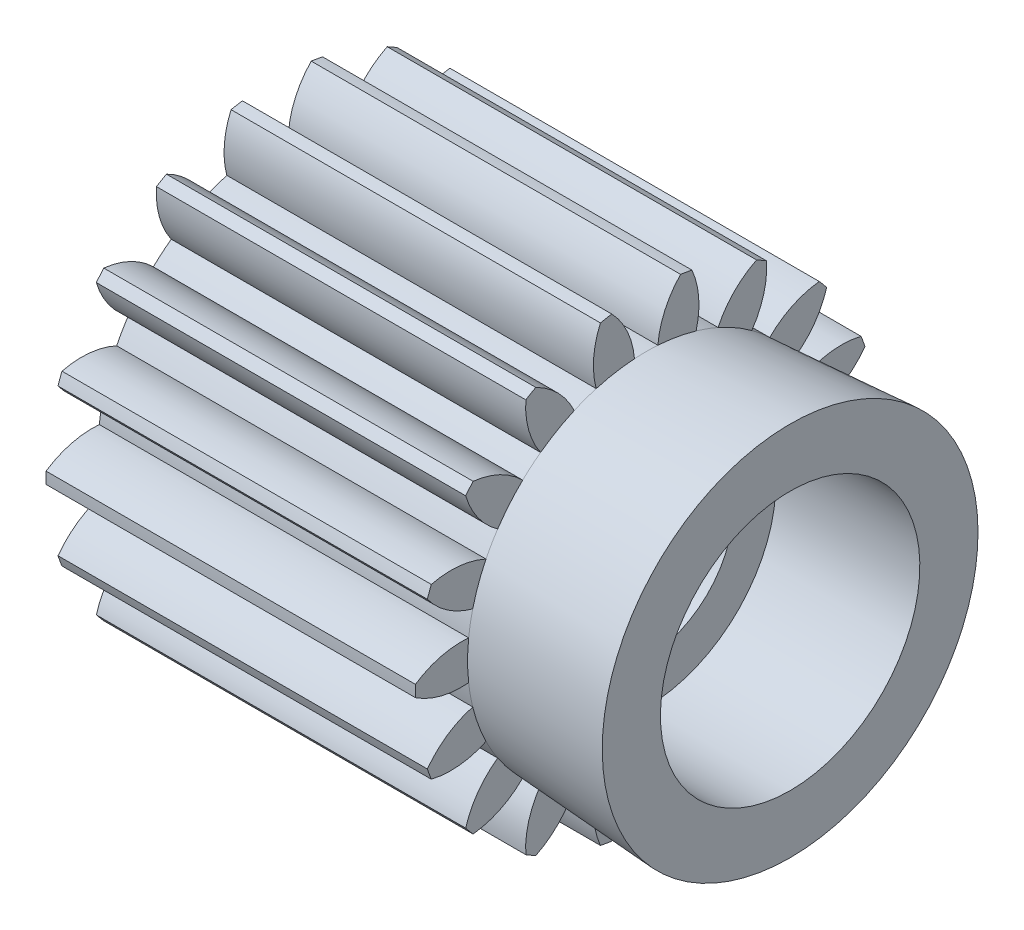
SolidWorks part; units mm, degrees
ref_plane "Plane1" through (0, 0, 0) normal (0, 0, 1) x (1, 0, 0)
ref_plane "Plane2" through (0, 0, 0) normal (0, 1, 0) x (1, 0, 0)
ref_plane "Plane3" through (0, 0, 0) normal (1, 0, 0) x (0, 0, -1)
sketch "HoldingSke" plane through (0, 0, 0) normal (0, 1, 0) x (1, 0, 0)
  line L0 (0, 0) -> (773.0187, -251.169)
  line L1 (-15, 0) -> (100, 0) construction
  line L2 (0, 0) -> (-2.1039, 2.3779)
  line L3 (0, 0) -> (-11.863, 4.5341)
  line L4 (0, 0) -> (8.2133, 2.6687)
  line L5 (0, 0) -> (-47.5972, -17.7524)
  line L6 (0, 0) -> (-10.5278, -7.1032)
  line L7 (-2.1039, 2.3779) -> (8.8308, 51.9871)
  line L8 (-76.2, 54.61) -> (-69.596, 54.61)
  line L9 (-71.009, 38.7566) -> (-53.1078, 45.2721)
  line L10 (-76.2, 71.12) -> (104.1128, 71.12)
  line L11 (0, 0) -> (-12.7, 0)
  line L12 (-76.2, 101.6) -> (-76.1716, 101.6)
  line L13 (24.9733, 27.94) -> (52.9518, 28.4284)
  line L14 (24.9733, 27.94) -> (25.0241, 27.9398)
  line L15 (24.9733, 27.94) -> (100.4021, 29.52)
  circle A0 centre (0, 0) radius 3.175
  circle A1 centre (0, 0) radius 6.1404
  circle A2 centre (0, 0) radius 38.1
  circle A3 centre (0, 0) radius 3.175
  dimension "MHD" = 12.2809
  dimension "Hub_dia" = 76.2
  dimension "Bore" = 6.35
  dimension "MBD" = 6.35
  dimension "Num_teeth" = 18
  dimension "Pitch" = 812.8
  dimension "Overall_len" = 50.8
  dimension "Show_teeth" = 18
  dimension "Thickness" = 12.7
  dimension "OAL" = 50.8001
  dimension "T_dim" = 6.604
  dimension "Ap" = 20
  dimension "H" = 19.05
  dimension "Pitch_radius" = 180.3128
  dimension "Width" = 12.7
  dimension "Backlash" = 0.0284
  dimension "Addendum_fac" = 1
  dimension "Dedendum_fac" = 1.2
  dimension "Clearance_fac" = 0.2
  dimension "Dedendum_add" = 0.0508
sketch "BasProSke" plane through (0, 0, 0) normal (0, 1, 0) x (1, 0, 0)
  line L0 (-10, 0) -> (60, 0) construction
  line L1 (0, 0) -> (0, 7.9375)
  line L2 (0, 0) -> (12.7, 0)
  line L3 (12.7, 0) -> (12.7, 7.9375)
  line L4 (12.7, 7.9375) -> (0, 7.9375)
  dimension "Thickness" = 12.7
  dimension "Diameter" = 15.875
revolve "Base-Revolve" add sketch "BasProSke" angle 360 about L0
sketch "TooCutSke" plane through (0, 0, 0) normal (1, 0, 0) x (0, 0, -1)
  line L1 (0, 0) -> (0, 107) construction
  line L2 (0, 0) -> (-0.6724, 7.112) construction
  line L3 (0, 0) -> (-2.473, 14.0251) construction
  line L4 (-0.6724, 7.112) -> (-1.2365, 7.0126) construction
  arc A0 (0.4018, 6.1273) -> (-0.4018, 6.1273) centre (0, 0) ccw
  arc A1 (1.2039, 7.8714) -> (-1.2039, 7.8714) centre (0, 0) ccw
  circle A2 centre (0, 0) radius 7.1438 construction
  circle A3 centre (0, 0) radius 6.7129 construction
  arc A4 (-0.4018, 6.1273) -> (-1.2039, 7.8714) centre (-3.2481, 5.8748) ccw
  arc A5 (1.2039, 7.8714) -> (0.4018, 6.1273) centre (3.2481, 5.8748) ccw
  dimension "Root_dia" = 12.2809
  dimension "Overcut_dia" = 15.9258
  dimension "Pitch_dia" = 14.2875
  dimension "Base_dia" = 13.4259
  dimension "Flank_rad" = 2.8575
  dimension "Half_ang" = 10
  dimension "Half_CT" = 0.5728
extrude "ToothCut" cut sketch "TooCutSke" along normal through all
fillet "Breaks" [suppressed] radius 0.0159
fillet "RootFillets" [suppressed] radius 0.2095
pattern_circular "TeethCuts" count 18 every 20 about axis through (-10, 0, 0) along (1, 0, 0) of "ToothCut", "RootFillets", "Breaks"
sketch "HubNeaOneSke" plane through (0, 0, 0) normal (-1, 0, 0) x (0, 0, 1)
  circle A0 centre (0, 0) radius 6.1404
  dimension "Diameter" = 12.2809
extrude "HubNearOne" [suppressed] add sketch "HubNeaOneSke" along normal blind 38.1001
sketch "HubNeaBotSke" plane through (0, 0, 0) normal (-1, 0, 0) x (0, 0, 1)
  circle A0 centre (0, 0) radius 6.1404
  dimension "Diameter" = 12.2809
extrude "HubNearBoth" [suppressed] add sketch "HubNeaBotSke" along normal blind 19.05
ref_plane "FarPln" through (12.7, 0, 0) normal (1, 0, 0) x (0, 0, -1)
sketch "HubFarSke" plane through (12.7, 0, 0) normal (1, 0, 0) x (0, 0, -1)
  circle A0 centre (0, 0) radius 6.1404
  dimension "Diameter" = 12.2809
extrude "HubFar" [suppressed] add sketch "HubFarSke" along normal blind 19.05
sketch "BorSke" plane through (0, 0, 0) normal (1, 0, 0) x (0, 0, -1)
  circle A0 centre (0, 0) radius 3
  dimension "D1" = 6
extrude "Bore" cut sketch "BorSke" along normal mid plane 101.6001
sketch "KeySke" plane through (0, 0, 0) normal (1, 0, 0) x (0, 0, -1)
  line L0 (-0.127, 0) -> (-0.127, 3.429)
  line L1 (-0.127, 3.429) -> (0.127, 3.429)
  line L2 (0.127, 3.429) -> (0.127, 0)
  line L3 (0, 0) -> (0, 34) construction
  line L4 (-0.127, 0) -> (0.127, 0)
  dimension "Offset" = 3.429
  dimension "Width" = 0.254
extrude "Keyway" [suppressed] cut sketch "KeySke" along normal mid plane 101.6001
pattern_circular "Keyway2" [suppressed] count 2 every 90 about axis through (-10, 0, 0) along (1, 0, 0)
sketch "Sketch1" plane through (0, 0, 0) normal (0, 0, 1) x (1, 0, 0)
  line L0 (12.7, 6.1405) -> (17.65, 6.46)
  line L1 (17.65, 6.46) -> (17.65, 4.46)
  line L2 (17.65, 4.46) -> (12.7, 4.46)
  line L3 (12.7, 4.9483) -> (12.7, 5.2527) construction
  line L4 (12.7, 0) -> (13.683, 0) construction
  line L5 (12.7, -0.1987) -> (12.7, 0.1987) construction
  line L6 (12.7, 4.46) -> (12.7, 6.1405)
  line L7 (12.7, 5.8952) -> (12.7, 7.78) construction
  point P3 (0, 0)
  point P8 (12.7, 7.2775)
  point P16 (12.7, 5.9593)
  point P18 (17.6948, 6.46)
  dimension "D1" = 4.46
  dimension "D2" = 2
  dimension "D3" = 4.95
revolve "Revolve1" add sketch "Sketch1" angle 360 about L4
equation "' \"Pitch@HoldingSke\" = 4"
equation "' \"Num_teeth@HoldingSke\" = 12"
equation "' \"Ap@HoldingSke\" =  20"
equation "' \"Ap@HoldingSke\" = 20"
equation "' \"Width@HoldingSke\" = 0.5"
equation "' \"Hub_dia@HoldingSke\"= 1"
equation "' \"Hub_dia@HoldingSke\" = 1"
equation "' \"Overall_len@HoldingSke\" = 1.0"
equation "' \"Bore@HoldingSke\" = 0.75"
equation "' \"T_dim@HoldingSke\" = 0.85"
equation "' \"Width@KeySke\" = 0.25"
equation "' \"Show_teeth@HoldingSke\" = 13"
equation "' \"Backlash@HoldingSke\" = 0.009"
equation "' \"Addendum_fac@HoldingSke\" = 1.0"
equation "' \"Dedendum_fac@HoldingSke\" = 1.25"
equation "' \"Dedendum_add@HoldingSke\" = 0.00005"
equation "' \"Clearance_fac@HoldingSke\" = 0.25"
equation "' \"Pitch@HoldingSke\" = 0.5"
equation "' \"Num_teeth@HoldingSke\" = 23"
equation "' \"Show_teeth@HoldingSke\" = 23"
equation "' \"Backlash@HoldingSke\" = 0.0375"
equation "\"Overcut_dia@TooCutSke\" = (\"Num_teeth@HoldingSke\" + 2 * \"Addendum_fac@HoldingSke\") / \"Pitch@HoldingSke\" + 0.002"
equation "\"Pitch_dia@TooCutSke\" = \"Num_teeth@HoldingSke\" / \"Pitch@HoldingSke\""
equation "\"Base_dia@TooCutSke\" = \"Num_teeth@HoldingSke\" / \"Pitch@HoldingSke\" * cos((\"Ap@HoldingSke\"  * 3.14159265 / 180))"
equation "\"Root_dia@TooCutSke\" = (\"Num_teeth@HoldingSke\" + 2) / \"Pitch@HoldingSke\" - 2 * (\"Addendum_fac@HoldingSke\" + \"Dedendum_fac@HoldingSke\") / \"Pitch@HoldingSke\" - \"Dedendum_add@HoldingSke\" * 2"
equation "\"Half_ang@TooCutSke\" = 180 / \"Num_teeth@HoldingSke\""
equation "\"Half_CT@TooCutSke\" = \"Num_teeth@HoldingSke\" / \"Pitch@HoldingSke\" * sin((3.14159265 / 2 / \"Num_teeth@HoldingSke\")) / 2 - 7 * \"Backlash@HoldingSke\" / 4"
equation "\"Flank_rad@TooCutSke\" = \"Num_teeth@HoldingSke\" / \"Pitch@HoldingSke\" / 5"
equation "\"Radius@RootFillets\" = \"Clearance_fac@HoldingSke\" / \"Pitch@HoldingSke\" + \"Dedendum_add@HoldingSke\""
equation "\"Break_rad@Breaks\" = 0.02 / \"Pitch@HoldingSke\""
equation "\"Thickness@HoldingSke\" = \"Width@HoldingSke\""
equation "\"OAL@HoldingSke\" = \"Thickness@HoldingSke\""
equation "\"MHD@HoldingSke\" = (\"Num_teeth@HoldingSke\" + 2) / \"Pitch@HoldingSke\" - 2 * (\"Addendum_fac@HoldingSke\" + \"Dedendum_fac@HoldingSke\")  / \"Pitch@HoldingSke\" - \"Dedendum_add@HoldingSke\" * 2"
equation "\"MBD@HoldingSke\" = (\"Num_teeth@HoldingSke\" + 2) / \"Pitch@HoldingSke\" - 2 * (\"Addendum_fac@HoldingSke\" + \"Dedendum_fac@HoldingSke\")  / \"Pitch@HoldingSke\" - \"Dedendum_add@HoldingSke\" * 2 - 0.002"
equation "\"MHD@HoldingSke\" = ((sgn( \"MHD@HoldingSke\" - \"Hub_dia@HoldingSke\" )-1)*( \"MHD@HoldingSke\" - \"Hub_dia@HoldingSke\" ))/-2+ \"Hub_dia@HoldingSke\""
equation "\"MBD@HoldingSke\" = ((sgn( \"MBD@HoldingSke\" - \"Bore@HoldingSke\" )-1)*( \"MBD@HoldingSke\" - \"Bore@HoldingSke\" ))/-2+ \"Bore@HoldingSke\""
equation "\"OAL@HoldingSke\" = ((sgn( \"OAL@HoldingSke\" - \"Overall_len@HoldingSke\" )+1)*( \"OAL@HoldingSke\" - \"Overall_len@HoldingSke\" ))/2 + \"Overall_len@HoldingSke\" + 0.000002"
equation "\"Num_teeth@TeethCuts\" = int( \"Show_teeth@HoldingSke\" ) + 1"
equation "\"Num_teeth@TeethCuts\" = ((sgn( \"Num_teeth@TeethCuts\" - \"Num_teeth@HoldingSke\" )-1)*( \"Num_teeth@TeethCuts\" - \"Num_teeth@HoldingSke\" ))/-2+ \"Num_teeth@HoldingSke\""
equation "\"Num_teeth@TeethCuts\" = ((sgn( \"Num_teeth@TeethCuts\" - 2.0)+1)*( \"Num_teeth@TeethCuts\" - 2.0))/2 +2.0"
equation "\"Angle@TeethCuts\" = 360.0 / \"Num_teeth@HoldingSke\""
equation "\"Diameter@BasProSke\" = (\"Num_teeth@HoldingSke\" + 2 * \"Addendum_fac@HoldingSke\") / \"Pitch@HoldingSke\""
equation "\"Thickness@BasProSke\"  = \"Thickness@HoldingSke\""
equation "' \"Fillet_rad@BasProSke\" =  \"Thickness@HoldingSke\" * 0.05"
equation "' \"Fillet_rad@BasProSke\" = \"Thickness@HoldingSke\" * 0.05"
equation "\"MHD@HoldingSke\" = ((sgn( \"MHD@HoldingSke\" - \"Root_dia@TooCutSke\" )-1)*( \"MHD@HoldingSke\" - \"Root_dia@TooCutSke\" ))/-2+ \"Root_dia@TooCutSke\""
equation "\"Diameter@HubNeaOneSke\" = \"MHD@HoldingSke\""
equation "\"Length@HubNearOne\" = \"OAL@HoldingSke\" - \"Thickness@BasProSke\""
equation "\"Diameter@HubNeaBotSke\" = \"MHD@HoldingSke\""
equation "\"Length@HubNearBoth\" = ( \"OAL@HoldingSke\" - \"Thickness@BasProSke\" ) / 2.0"
equation "\"Thickness@FarPln\" = \"Thickness@BasProSke\""
equation "\"Diameter@HubFarSke\" = \"MHD@HoldingSke\""
equation "\"Length@HubFar\" = ( \"OAL@HoldingSke\" - \"Thickness@BasProSke\" ) / 2.0"
equation "\"D1@Bore\" = \"OAL@HoldingSke\" * 2.0"
equation "\"D1@Keyway\" = \"OAL@HoldingSke\" * 2.0"
equation "\"Offset@KeySke\" = \"T_dim@HoldingSke\" - \"MBD@HoldingSke\" / 2.0"
